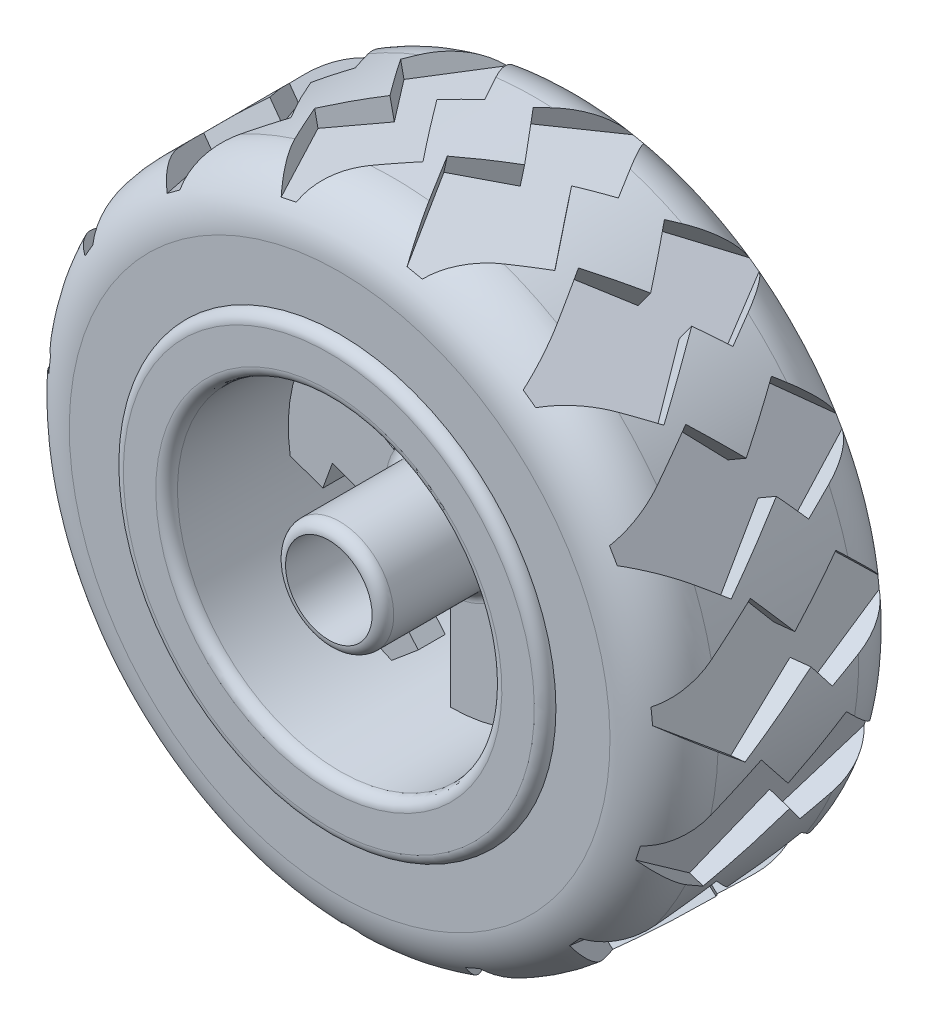
SolidWorks part; units mm, degrees
ref_plane "Alzado" through (0, 0, 0) normal (0, 0, 1) x (1, 0, 0)
ref_plane "Planta" through (0, 0, 0) normal (0, 1, 0) x (1, 0, 0)
ref_plane "Vista lateral" through (0, 0, 0) normal (1, 0, 0) x (0, 0, -1)
sketch "Croquis1" plane through (0, 0, 0) normal (1, 0, 0) x (0, 0, -1)
  line L0 (0, 0) -> (-11.5, 0)
  line L1 (-12.5, 1) -> (-12.5, 4)
  line L2 (-11.5, 5) -> (-2.25, 5)
  line L3 (-1.25, 6) -> (-1.25, 15)
  line L4 (-1.25, 15) -> (-11.5, 15)
  line L5 (-12.5, 16) -> (-12.5, 19)
  line L6 (-11.5, 20) -> (11.5, 20)
  line L7 (0, 0) -> (11.5, 0)
  line L8 (12.5, 1) -> (12.5, 4)
  line L9 (11.5, 5) -> (2.25, 5)
  line L10 (1.25, 6) -> (1.25, 15)
  line L11 (1.25, 15) -> (11.5, 15)
  line L12 (12.5, 16) -> (12.5, 19)
  arc A0 (2.25, 5) -> (1.25, 6) centre (2.25, 6) cw
  arc A1 (-2.25, 5) -> (-1.25, 6) centre (-2.25, 6) ccw
  arc A2 (11.5, 0) -> (12.5, 1) centre (11.5, 1) ccw
  arc A3 (12.5, 4) -> (11.5, 5) centre (11.5, 4) ccw
  arc A4 (-11.5, 0) -> (-12.5, 1) centre (-11.5, 1) cw
  arc A5 (-12.5, 4) -> (-11.5, 5) centre (-11.5, 4) cw
  arc A6 (11.5, 15) -> (12.5, 16) centre (11.5, 16) ccw
  arc A7 (11.5, 20) -> (12.5, 19) centre (11.5, 19) cw
  arc A8 (-11.5, 15) -> (-12.5, 16) centre (-11.5, 16) cw
  arc A9 (-12.5, 19) -> (-11.5, 20) centre (-11.5, 19) cw
  point P16 (1.25, 5)
  point P19 (-1.25, 5)
  point P22 (12.5, 0)
  point P25 (12.5, 5)
  point P28 (-12.5, 0)
  point P31 (-12.5, 5)
  point P38 (-12.5, 15)
  point P41 (-12.5, 20)
  point P42 (5.75, 0)
  dimension "D7" = 1
  dimension "D1" = 12.5
  dimension "D2" = 5
  dimension "5" = 5
  dimension "D3" = 11.25
  dimension "D4" = 11.25
  dimension "D5" = 12.5
  dimension "D6" = 11.25
  dimension "D8" = 20
revolve "Revolución1" add sketch "Croquis1" angle 360 about L7
sketch "Croquis2" plane through (0, 0, 12.5) normal (0, 0, 1) x (1, 0, 0)
  circle A0 centre (0, 0) radius 4
  dimension "D1" = 8
extrude "Cortar-Extruir1" cut sketch "Croquis2" against normal through all
sketch "Croquis3" plane through (0, 0, 1.25) normal (0, 0, 1) x (1, 0, 0)
  line L0 (0, 0) -> (0, 15) construction
  line L27 (0, 6) -> (0, 15)
  line L28 (0, 6) -> (4.6638, 9.9134)
  line L29 (4.6638, 9.9134) -> (2.9856, 11.9134)
  line L30 (2.9856, 11.9134) -> (5.4448, 13.9769)
  line L31 (11.8102, 3.3711) -> (14.8268, 2.2731)
  line L32 (10.9172, 0.9177) -> (11.8102, 3.3711)
  line L33 (5.1962, 3) -> (10.9172, 0.9177)
  line L34 (5.1962, 3) -> (12.9904, 7.5)
  line L35 (8.8245, -8.5424) -> (9.382, -11.7038)
  line L36 (6.2534, -8.9957) -> (8.8245, -8.5424)
  line L37 (5.1962, -3) -> (6.2534, -8.9957)
  line L38 (5.1962, -3) -> (12.9904, -7.5)
  line L39 (-2.9856, -11.9134) -> (-5.4448, -13.9769)
  line L40 (-4.6638, -9.9134) -> (-2.9856, -11.9134)
  line L41 (0, -6) -> (-4.6638, -9.9134)
  line L42 (0, -6) -> (0, -15)
  line L43 (-11.8102, -3.3711) -> (-14.8268, -2.2731)
  line L44 (-10.9172, -0.9177) -> (-11.8102, -3.3711)
  line L45 (-5.1962, -3) -> (-10.9172, -0.9177)
  line L46 (-5.1962, -3) -> (-12.9904, -7.5)
  line L47 (-8.8245, 8.5424) -> (-9.382, 11.7038)
  line L48 (-6.2534, 8.9957) -> (-8.8245, 8.5424)
  line L49 (-5.1962, 3) -> (-6.2534, 8.9957)
  line L50 (-5.1962, 3) -> (-12.9904, 7.5)
  circle A23 centre (0, 0) radius 15 construction
  circle A24 centre (0, 0) radius 6 construction
  arc A25 (0, 15) -> (5.4448, 13.9769) centre (0, 0) cw
  arc A26 (12.9904, 7.5) -> (14.8268, 2.2731) centre (0, 0) cw
  arc A27 (12.9904, -7.5) -> (9.382, -11.7038) centre (0, 0) cw
  arc A28 (0, -15) -> (-5.4448, -13.9769) centre (0, 0) cw
  arc A29 (-12.9904, -7.5) -> (-14.8268, -2.2731) centre (0, 0) cw
  arc A30 (-12.9904, 7.5) -> (-9.382, 11.7038) centre (0, 0) cw
  point P28 (4.2013, 18.0701)
  point P41 (0, 0)
  point P42 (0, 0)
  dimension "D1" = 50
  dimension "D2" = 2
  dimension "D3" = 3.2102
  dimension "D4" = 6
extrude "Cortar-Extruir2" cut sketch "Croquis3" against normal through all
ref_plane "Plano1" through (0, 0, 0) normal (1, 0, 0) x (0, 0, -1)
sketch "Croquis4" plane through (0, 0, 0) normal (1, 0, 0) x (0, 0, -1)
  line L0 (-11.5, 20) -> (11.5, 20)
  line L1 (-11.5, 20) -> (-11.5, -20) construction
  line L2 (11.5, 20) -> (11.5, 25)
  line L3 (6.5, 30) -> (-6.5, 30)
  line L4 (-11.5, 25) -> (-11.5, 20)
  line L5 (0, 0) -> (12.5, 0) construction
  line L6 (12.5, -19) -> (12.5, 19) construction
  line L7 (12.5, 0) -> (-12.5, 0) construction
  line L8 (-12.5, 19) -> (-12.5, -19) construction
  arc A0 (-11.5, 20) -> (-12.5, 19) centre (-11.5, 19) ccw construction
  arc A1 (11.5, 25) -> (6.5, 30) centre (6.5, 25) ccw
  arc A2 (-6.5, 30) -> (-11.5, 25) centre (-6.5, 25) ccw
  point P14 (-11.5, 30)
  dimension "D2" = 5
  dimension "D1" = 10
revolve "Revolución2" add sketch "Croquis4" angle 360 about L7
ref_plane "Plano2" through (0, -30, 0) normal (0, -1, 0) x (-1, 0, 0)
sketch "Croquis5" plane through (0, -30, 0) normal (0, -1, 0) x (-1, 0, 0)
  line L0 (0, 11.2116) -> (0, -11.5) construction
  line L1 (-20, -11.5) -> (20, -11.5) construction
  line L2 (0, -11.5) -> (-5.5404, -2.2608)
  line L3 (-5.5404, -2.2608) -> (-1.6294, 0.9699)
  line L4 (-1.6294, 0.9699) -> (-5.4664, 5.615)
  line L5 (0, 11.2116) -> (-5.4664, 5.615)
  line L7 (0, 11.2116) -> (4.1122, 4.0734)
  line L8 (4.1122, 4.0734) -> (1.6234, 2.1305)
  line L9 (1.6234, 2.1305) -> (6.2847, -3.8406)
  line L10 (6.2847, -3.8406) -> (0, -11.5)
  point P4 (0, 11.2116)
  point P11 (-6.5174, 4.5389)
  point P12 (-1.6294, 0.9699)
  point P13 (0, 0)
  point P14 (8.6899, 3.7631)
  point P15 (6.2847, -3.8406)
  point P16 (4.1122, 4.0734)
extrude "Cortar-Extruir3" cut sketch "Croquis5" against normal blind 2
pattern_circular "MatrizC1" count 15 over 360 about axis through (0, 0, 0) along (0, 0, 1) of "Cortar-Extruir3"
